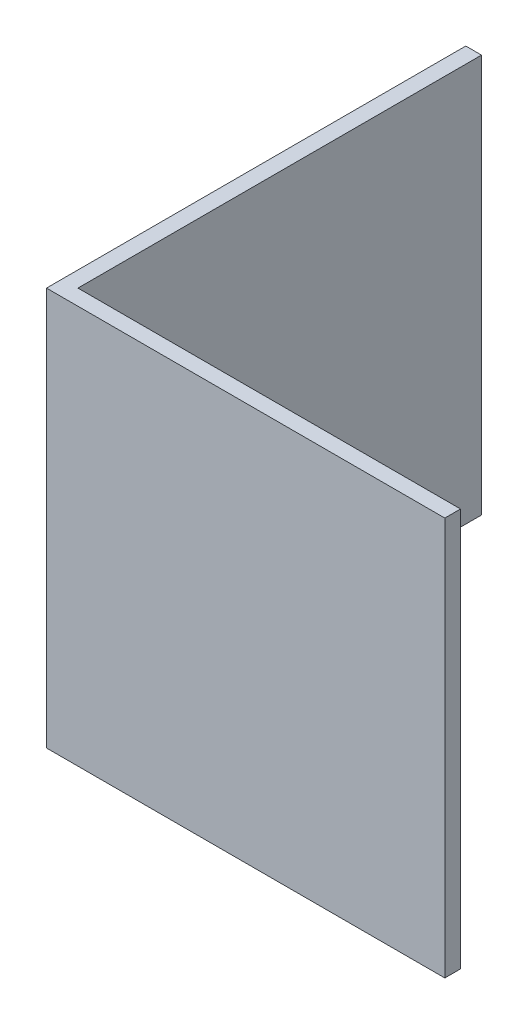
SolidWorks part; units mm, degrees
material "1060 Сплав"
ref_plane "Спереди" through (0, 0, 0) normal (0, 0, 1) x (1, 0, 0)
ref_plane "Сверху" through (0, 0, 0) normal (0, 1, 0) x (1, 0, 0)
ref_plane "Справа" through (0, 0, 0) normal (1, 0, 0) x (0, 0, -1)
sketch "Эскиз1" plane through (0, 0, 0) normal (0, 1, 0) x (1, 0, 0)
  line L0 (0, 0) -> (0, 20)
  line L1 (0, 20) -> (0.75, 20)
  line L2 (0.75, 20) -> (0.75, 0.75)
  line L3 (0.75, 0.75) -> (20, 0.75)
  line L4 (20, 0.75) -> (20, 0)
  line L5 (20, 0) -> (0, 0)
  dimension "D1" = 0.75
  dimension "D2" = 20
extrude "Бобышка-Вытянуть1" add sketch "Эскиз1" along normal blind 19
sketch "Эскиз2" plane through (20, 0, 0) normal (1, 0, 0) x (0, 0, -1)
  line L4 (0, 0) -> (0.75, 0)
  line L5 (0.75, 0) -> (0.75, 19)
  line L6 (0.75, 19) -> (0, 19)
  line L7 (0, 19) -> (0, 0)
  line L8 (0, 0) -> (0.75, 0)
  line L9 (0.75, 0) -> (0.75, 19)
  line L10 (0.75, 19) -> (0, 19)
  line L11 (0, 19) -> (0, 0)
  dimension "D1" = 0
extrude "Вырез-Вытянуть1" cut sketch "Эскиз2" against normal blind 1
